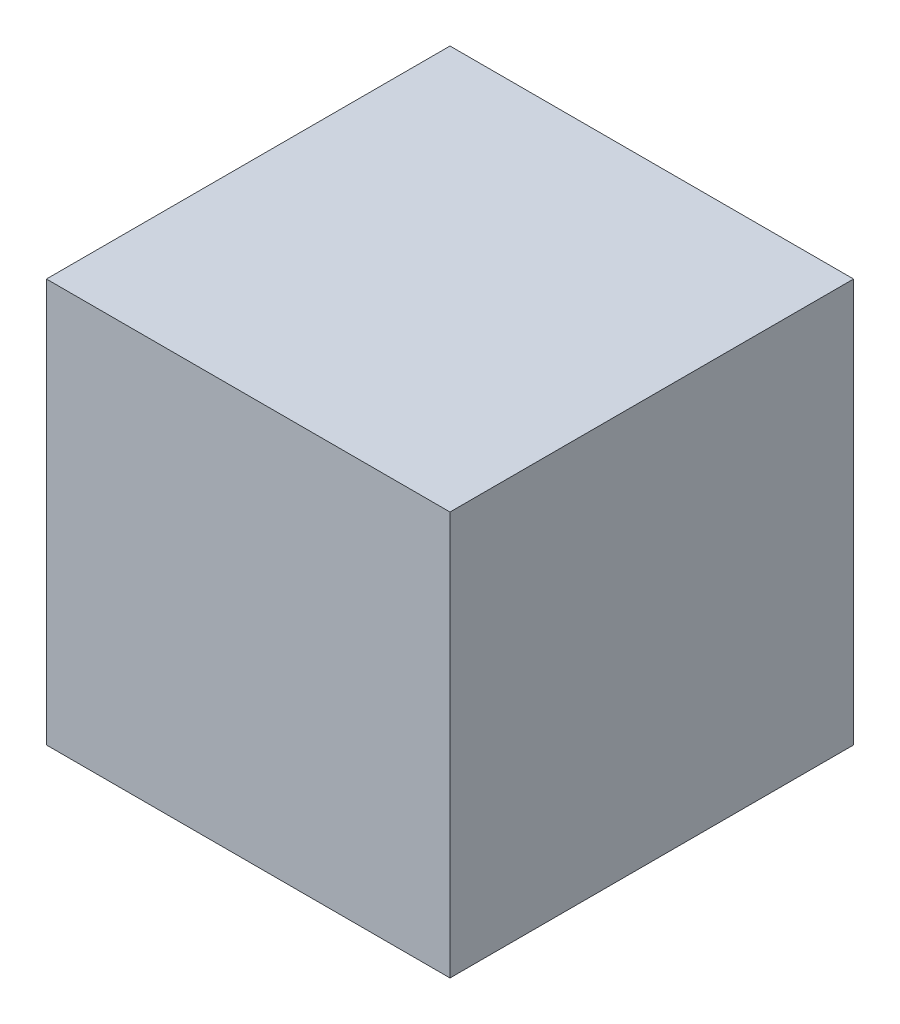
SolidWorks part; units mm, degrees
ref_plane "Front Plane" through (0, 0, 0) normal (0, 0, 1) x (1, 0, 0)
ref_plane "Top Plane" through (0, 0, 0) normal (0, 1, 0) x (1, 0, 0)
ref_plane "Right Plane" through (0, 0, 0) normal (1, 0, 0) x (0, 0, -1)
sketch "Sketch1" plane through (0, 0, 0) normal (0, 0, 1) x (1, 0, 0)
  line L1 (-20.9486, 25.0353) -> (9.0514, 25.0353)
  line L2 (-20.9486, 25.0353) -> (-20.9486, -4.9647)
  line L3 (-20.9486, -4.9647) -> (9.0514, -4.9647)
  line L4 (9.0514, 25.0353) -> (9.0514, -4.9647)
extrude "Boss-Extrude1" add sketch "Sketch1" along normal blind 30
